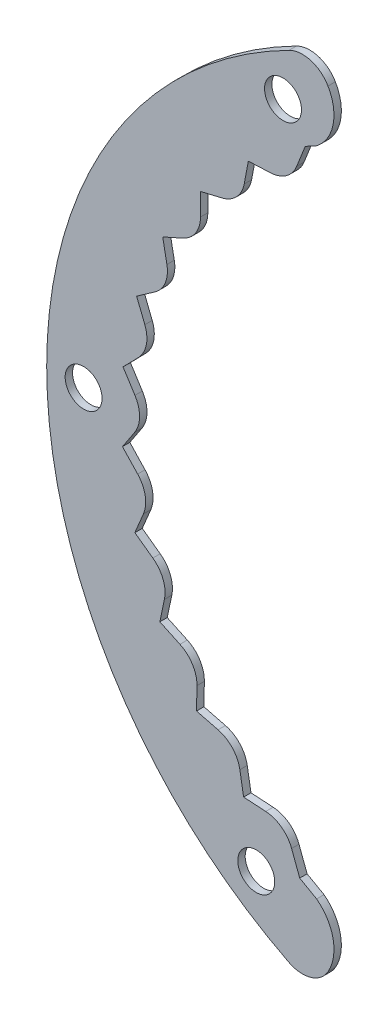
SolidWorks part; units mm, degrees
material "3003 Alaşım"
ref_plane "Ön Düzlem" through (0, 0, 0) normal (0, 0, 1) x (1, 0, 0)
ref_plane "Üst Düzlem" through (0, 0, 0) normal (0, 1, 0) x (1, 0, 0)
ref_plane "Sağ Düzlem" through (0, 0, 0) normal (1, 0, 0) x (0, 0, -1)
sketch "Çizim1" plane through (0, 0, 0) normal (0, 0, 1) x (1, 0, 0)
  line L0 (-50, 0) -> (-25, 0) construction
  line L1 (-25, 74.7114) -> (-25, -53.9079) construction
  line L2 (-23.4461, -44.162) -> (-25.7378, -42.8669)
  line L3 (-25, 43.3013) -> (-26.1465, 40.3921)
  line L10 (-32.6937, 37.73) -> (-33.2521, 34.7773)
  line L11 (-32.6937, 37.73) -> (-29.6915, 37.8626)
  line L12 (-39.1845, 30.9355) -> (-36.2603, 31.6283)
  line L13 (-39.1845, 30.9355) -> (-39.1797, 27.9304)
  line L14 (-44.2872, 23.0451) -> (-41.5446, 24.2736)
  line L15 (-44.2872, 23.0451) -> (-43.7194, 20.0942)
  line L16 (-47.8209, 14.3384) -> (-45.3571, 16.059)
  line L17 (-47.8209, 14.3384) -> (-46.7103, 11.546)
  line L18 (-49.6606, 5.1236) -> (-47.5629, 7.2754)
  line L19 (-49.6606, 5.1236) -> (-48.0464, 2.5889)
  line L20 (-49.7411, -4.2726) -> (-48.0837, -1.7658)
  line L21 (-49.7411, -4.2726) -> (-47.6805, -6.46)
  line L22 (-48.0594, -13.5175) -> (-46.9011, -10.7445)
  line L23 (-48.0594, -13.5175) -> (-45.6255, -15.28)
  line L24 (-44.6753, -22.2835) -> (-44.057, -19.3426)
  line L25 (-44.6753, -22.2835) -> (-41.9541, -23.5587)
  line L26 (-39.7084, -30.2601) -> (-39.6522, -27.2555)
  line L27 (-39.7084, -30.2601) -> (-36.7965, -31.0028)
  line L28 (-33.3349, -37.1647) -> (-33.8427, -34.2028)
  line L29 (-33.3349, -37.1647) -> (-30.3354, -37.3487)
  line L30 (-25.7378, -42.8669) -> (-26.8343, -39.9385)
  line L32 (-27.1796, -53.4909) -> (-27.1875, -53.4868)
  line L33 (-15, -47.697) -> (-15, -66.5436) construction
  line L35 (-25, -54.5436) -> (-25, -66.5436) construction
  arc A0 (-27.1796, 53.4909) -> (-27.1875, -53.4868) centre (0, 0) ccw
  arc A3 (-23.4461, 44.162) -> (-21.9062, 51.9296) centre (-27.0983, 48.9224) ccw
  arc A4 (-26.1465, 40.3921) -> (-29.6915, 37.8626) centre (-29.8679, 41.8587) cw
  arc A5 (-33.2521, 34.7773) -> (-36.2603, 31.6283) centre (-37.1824, 35.5206) cw
  arc A6 (-39.1797, 27.9304) -> (-41.5446, 24.2736) centre (-43.1797, 27.9241) cw
  arc A7 (-43.7194, 20.0942) -> (-45.3571, 16.059) centre (-47.6474, 19.3384) cw
  arc A8 (-46.7103, 11.546) -> (-47.5629, 7.2754) centre (-50.4271, 10.0677) cw
  arc A9 (-48.0464, 2.5889) -> (-48.0837, -1.7658) centre (-51.4203, 0.4403) cw
  arc A10 (-47.6805, -6.46) -> (-46.9011, -10.7445) centre (-50.592, -9.2028) cw
  arc A11 (-45.6255, -15.28) -> (-44.057, -19.3426) centre (-47.9715, -18.5198) cw
  arc A12 (-41.9541, -23.5587) -> (-39.6522, -27.2555) centre (-43.6515, -27.1807) cw
  arc A13 (-36.7965, -31.0028) -> (-33.8427, -34.2028) centre (-37.7852, -34.8787) cw
  arc A14 (-30.3354, -37.3487) -> (-26.8343, -39.9385) centre (-30.5803, -41.3412) cw
  arc A15 (-23.4461, 44.162) -> (-25, 43.3013) centre (0, 0) ccw
  arc A16 (-20.8333, 45.453) -> (-15, -47.697) centre (0, 0) ccw construction
  arc A19 (-25, 54.5436) -> (-25, -54.5436) centre (0, 0) ccw construction
  arc A21 (-27.1796, 53.4909) -> (-21.9062, 51.9296) centre (-25.3676, 49.9248) cw
  circle A26 centre (-31.6201, -45.0019) radius 2.5
  circle A27 centre (-55, 0) radius 2.5
  circle A28 centre (-28.0006, 47.3388) radius 2.5
  arc A30 (-23.4461, -44.162) -> (-21.9062, -51.9296) centre (-27.0983, -48.9224) cw
  arc A31 (-27.1796, -53.4909) -> (-21.9062, -51.9296) centre (-25.3676, -49.9248) ccw
  point P9 (-25, 0)
  point P69 (0, 0)
  dimension "D1" = 60
  dimension "D2" = 10
  dimension "D4" = 4
  dimension "D8" = 4
  dimension "D3" = 25
  dimension "D5" = 11
extrude "Yükseklik-Ekstrüzyon1" add sketch "Çizim1" along normal blind 1
